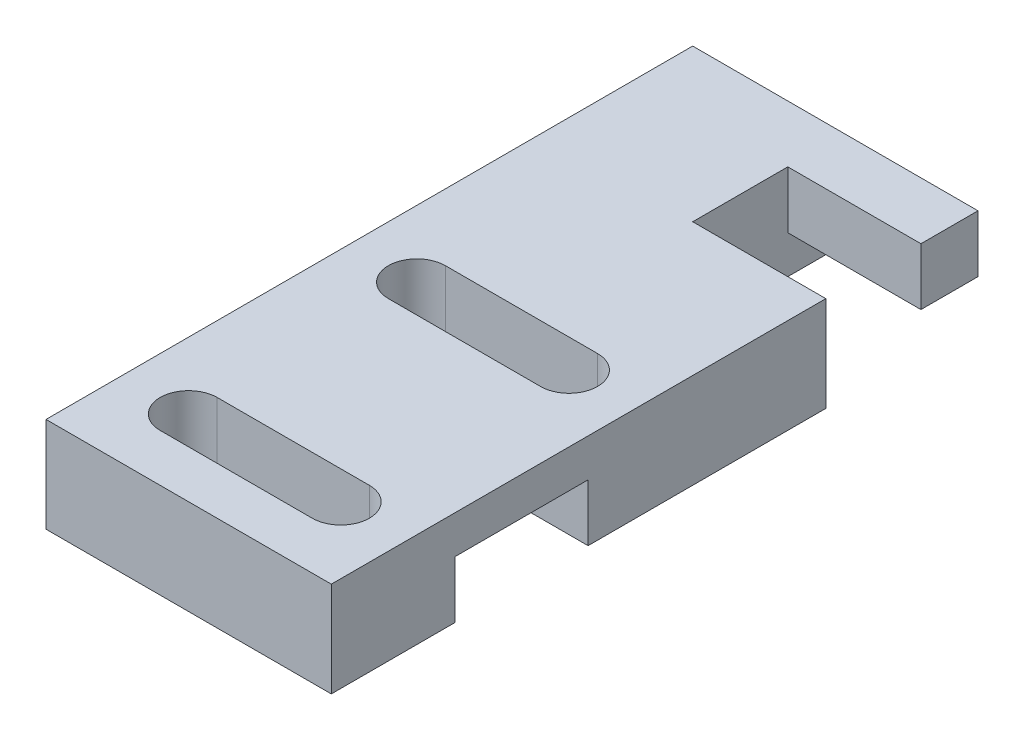
SolidWorks part; units mm, degrees
ref_plane "前视基准面" through (0, 0, 0) normal (0, 0, 1) x (1, 0, 0)
ref_plane "上视基准面" through (0, 0, 0) normal (0, 1, 0) x (1, 0, 0)
ref_plane "右视基准面" through (0, 0, 0) normal (1, 0, 0) x (0, 0, -1)
sketch "草图1" plane through (0, 0, 0) normal (0, 1, 0) x (1, 0, 0)
  line L0 (0, 34) -> (15, 34)
  line L1 (0, -55) -> (0, 55) construction
  line L2 (15, 34) -> (15, 0)
  line L3 (-55, 0) -> (55, 0) construction
  line L4 (15, 0) -> (0, 0)
  line L5 (0, 0) -> (0, 34)
  line L6 (3.5, 4) -> (11.5, 4) construction
  line L7 (3.5, 5.5) -> (11.5, 5.5)
  line L8 (3.5, 2.5) -> (11.5, 2.5)
  line L9 (15, 31) -> (8, 31)
  line L10 (3.5, 16) -> (11.5, 16) construction
  line L11 (3.5, 17.5) -> (11.5, 17.5)
  line L12 (3.5, 14.5) -> (11.5, 14.5)
  line L13 (8, 31) -> (8, 26)
  line L14 (8, 26) -> (15, 26)
  arc A0 (3.5, 5.5) -> (3.5, 2.5) centre (3.5, 4) ccw
  arc A1 (11.5, 2.5) -> (11.5, 5.5) centre (11.5, 4) ccw
  arc A2 (3.5, 17.5) -> (3.5, 14.5) centre (3.5, 16) ccw
  arc A3 (11.5, 14.5) -> (11.5, 17.5) centre (11.5, 16) ccw
  point P11 (7.5, 4)
  point P20 (7.5, 16)
  dimension "D3" = 1.5
  dimension "D6" = 1.5
  dimension "D1" = 34
  dimension "D2" = 15
  dimension "D4" = 8
  dimension "D5" = 8
  dimension "D7" = 7.5
  dimension "D8" = 7.5
  dimension "D9" = 4
  dimension "D10" = 5
  dimension "D11" = 12
  dimension "D12" = 3
  dimension "D13" = 8
extrude "凸台-拉伸1" add sketch "草图1" along normal blind 5
sketch "草图2" plane through (0, 0, 0) normal (-1, 0, 0) x (0, 0, 1)
  line L0 (0, -55) -> (0, 55) construction
  line L1 (-13.5, 3) -> (-6.5, 3)
  line L2 (-13.5, 3) -> (-13.5, 0)
  line L3 (-13.5, 0) -> (-6.5, 0)
  line L4 (-6.5, 3) -> (-6.5, 0)
  dimension "D1" = 3
  dimension "D2" = 7
  dimension "D3" = 6.5
extrude "切除-拉伸1" cut sketch "草图2" against normal through all
sketch "草图4" plane through (8, 0, 0) normal (1, 0, 0) x (0, 0, -1)
  line L0 (31, 5) -> (31, 0) construction
  line L1 (31, 2) -> (34, 2)
  line L2 (31, 2) -> (31, 0)
  line L3 (31, 0) -> (34, 0)
  line L4 (34, 2) -> (34, 0)
  line L5 (8.25, 0) -> (-8.25, 0) construction
  line L6 (34, 5) -> (34, 0) construction
  dimension "D1" = 2
extrude "切除-拉伸3" cut sketch "草图4" along normal blind 16
